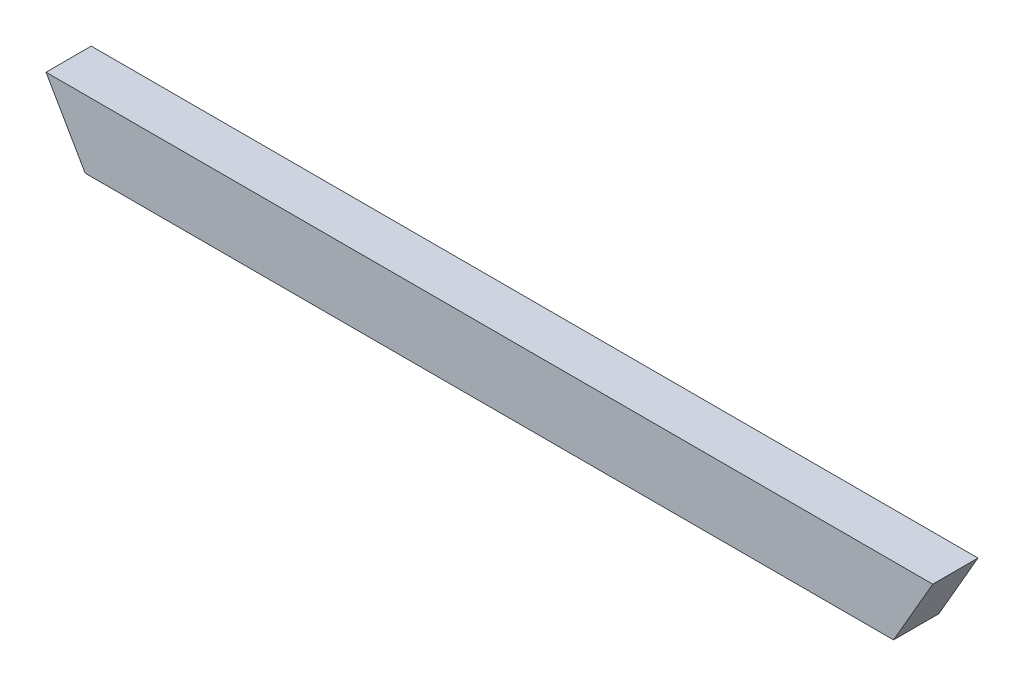
SolidWorks part; units mm, degrees
ref_plane "Front Plane" through (0, 0, 0) normal (0, 0, 1) x (1, 0, 0)
ref_plane "Top Plane" through (0, 0, 0) normal (0, 1, 0) x (1, 0, 0)
ref_plane "Right Plane" through (0, 0, 0) normal (1, 0, 0) x (0, 0, -1)
sketch "Sketch1" plane through (0, 0, 0) normal (0, 0, 1) x (1, 0, 0)
  line L0 (248.8682, 0) -> (237.8696, -19.05)
  line L1 (-248.8682, 19.05) -> (248.8682, 19.05) construction
  line L2 (-248.8682, 19.05) -> (-248.8682, -19.05) construction
  line L3 (-248.8682, -19.05) -> (248.8682, -19.05) construction
  line L4 (248.8682, 19.05) -> (248.8682, -19.05) construction
  line L5 (-248.8682, 19.05) -> (248.8682, -19.05) construction
  line L6 (-248.8682, -19.05) -> (248.8682, 19.05) construction
  line L7 (248.8682, 0) -> (259.8667, 19.05)
  line L8 (-215.8726, -19.05) -> (237.8696, -19.05)
  line L11 (-237.8696, 19.05) -> (259.8667, 19.05)
  line L12 (-237.8696, 19.05) -> (-215.8726, -19.05)
  point P0 (0, 0)
  dimension "D1" = 497.7363
  dimension "D2" = 38.1
  dimension "D3" = 21.997
extrude "Boss-Extrude1" add sketch "Sketch1" along normal blind 25.4
